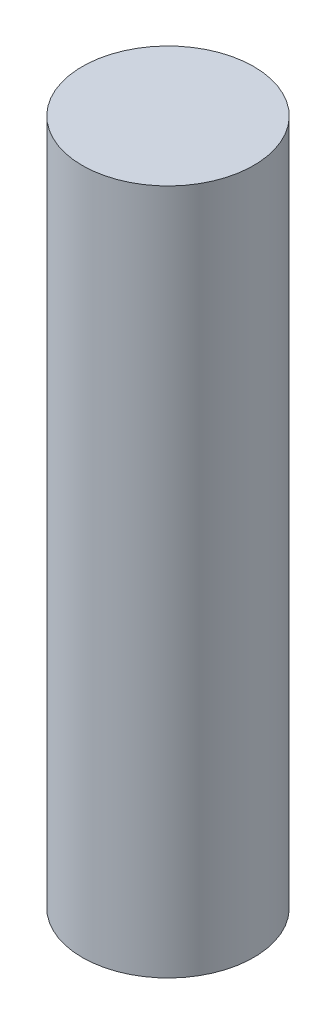
SolidWorks part; units mm, degrees
ref_plane "Front Plane" through (0, 0, 0) normal (0, 0, 1) x (1, 0, 0)
ref_plane "Top Plane" through (0, 0, 0) normal (0, 1, 0) x (1, 0, 0)
ref_plane "Right Plane" through (0, 0, 0) normal (1, 0, 0) x (0, 0, -1)
sketch "Sketch1" plane through (0, 0, 0) normal (0, 1, 0) x (1, 0, 0)
  circle A0 centre (0, 0) radius 1.5
  dimension "D1" = 3
extrude "Boss-Extrude1" add sketch "Sketch1" along normal blind 12
